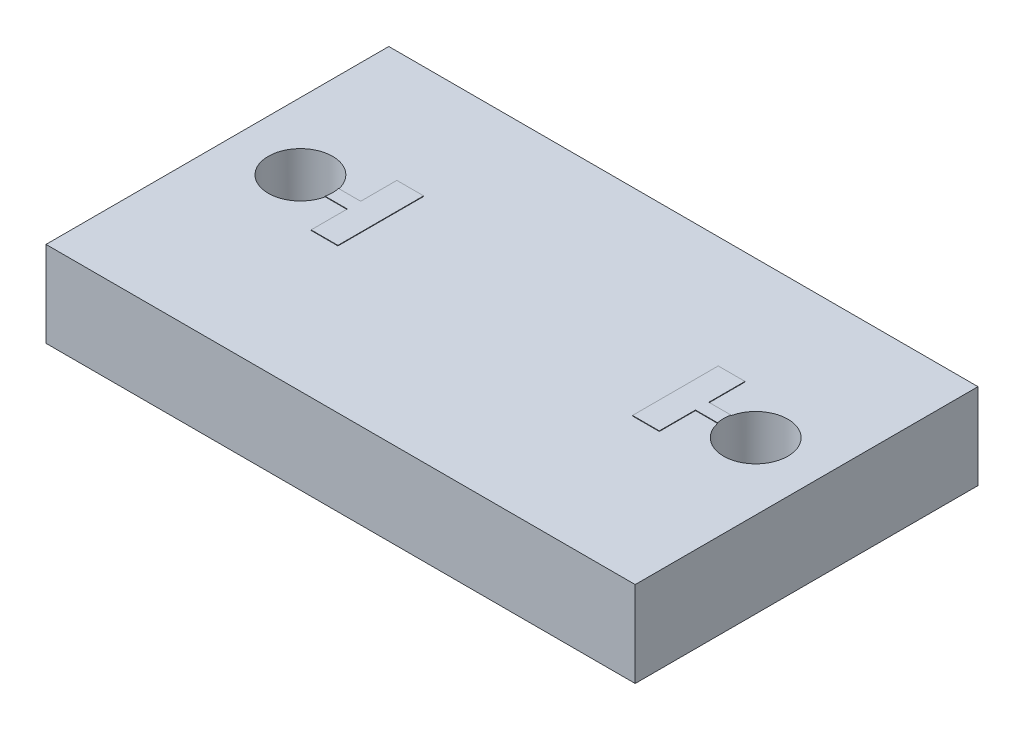
SolidWorks part; units mm, degrees
ref_plane "Front Plane" through (0, 0, 0) normal (0, 0, 1) x (1, 0, 0)
ref_plane "Top Plane" through (0, 0, 0) normal (0, 1, 0) x (1, 0, 0)
ref_plane "Right Plane" through (0, 0, 0) normal (1, 0, 0) x (0, 0, -1)
sketch "Sketch1" plane through (0, 0, 0) normal (0, 1, 0) x (1, 0, 0)
  line L1 (-5.5, -2) -> (5.5, -2)
  line L2 (-5.5, -2) -> (-5.5, 2)
  line L3 (-5.5, 2) -> (5.5, 2)
  line L4 (5.5, -2) -> (5.5, 2)
  line L5 (-5.5, -2) -> (5.5, 2) construction
  line L6 (-5.5, 2) -> (5.5, -2) construction
  point P0 (0, 0)
  dimension "D1" = 4
  dimension "D2" = 11
extrude "Boss-Extrude1" add sketch "Sketch1" along normal blind 1.6
sketch "Sketch2" plane through (0, 1.6, 0) normal (0, 1, 0) x (1, 0, 0)
  line L0 (0, -2) -> (0, 2) construction
  line L1 (-5.5, -2) -> (5.5, -2) construction
  line L2 (5.5, 2) -> (-5.5, 2) construction
  line L3 (-3.25, 0.8) -> (-2.75, 0.8)
  line L8 (0, 0) -> (3, 0)
  line L9 (-2.75, -0.8) -> (-2.75, 0.8)
  line L10 (3.25, -0.8) -> (2.75, -0.8)
  line L11 (3.25, -0.8) -> (3.25, 0.8)
  line L12 (3.25, 0.8) -> (2.75, 0.8)
  line L13 (2.75, -0.8) -> (2.75, 0.8)
  line L14 (3.25, -0.8) -> (2.75, 0.8) construction
  line L15 (3.25, 0.8) -> (2.75, -0.8) construction
  line L16 (-3.25, -0.8) -> (-2.75, -0.8)
  line L17 (-3.25, -0.8) -> (-3.25, 0.8)
  dimension "D3" = 3
  dimension "D4" = 0.5
  dimension "D5" = 1.6
sketch "Sketch3" plane through (0, 1.6, 0) normal (0, 1, 0) x (1, 0, 0)
  line L0 (0, -2) -> (0, 2) construction
  line L1 (4.25, 0) -> (4.25, 1) construction
  line L2 (3.65, 0) -> (3.65, 1)
  line L3 (4.85, 0) -> (4.85, 1)
  line L4 (-4.25, 0) -> (-4.25, 1) construction
  line L5 (-3.65, 0) -> (-3.65, 1)
  line L6 (-4.85, 0) -> (-4.85, 1)
  line L7 (5.5, 2) -> (-5.5, 2) construction
  line L8 (-5.5, -2) -> (5.5, -2) construction
  circle A0 centre (4.25, 0) radius 0.6
  circle A1 centre (-4.25, 0) radius 0.6
  arc A2 (3.65, 0) -> (4.85, 0) centre (4.25, 0) ccw
  arc A3 (4.85, 1) -> (3.65, 1) centre (4.25, 1) ccw
  arc A4 (-3.65, 0) -> (-4.85, 0) centre (-4.25, 0) cw
  arc A5 (-4.85, 1) -> (-3.65, 1) centre (-4.25, 1) cw
  point P10 (4.25, 0.5)
  point P17 (-4.25, 0.5)
  dimension "D1" = 1.2
  dimension "D5" = 1
  dimension "D2" = 1.25
  dimension "D3" = 4.25
  dimension "D4" = 1.2
extrude "Cut-Extrude1" cut sketch "Sketch3" against normal blind 1.6 contours A0 | A1
extrude "Boss-Extrude2" add sketch "Sketch2" along normal blind 0.01
sketch "Sketch4" plane through (0, 1.6, 0) normal (0, 1, 0) x (1, 0, 0)
  line L0 (3.25, -0.8) -> (3.25, 0.8) construction
  line L1 (5.25, -0.125) -> (3.25, -0.125)
  line L2 (5.25, -0.125) -> (5.25, 0.125)
  line L3 (5.25, 0.125) -> (3.25, 0.125)
  line L4 (3.25, -0.125) -> (3.25, 0.125)
  line L5 (5.25, -0.125) -> (3.25, 0.125) construction
  line L6 (5.25, 0.125) -> (3.25, -0.125) construction
  line L7 (0, 0) -> (0, 2) construction
  line L8 (5.5, 2) -> (-5.5, 2) construction
  line L9 (-5.25, 0.125) -> (-3.25, 0.125)
  line L10 (-3.25, -0.125) -> (-3.25, 0.125)
  line L11 (-5.25, -0.125) -> (-3.25, -0.125)
  line L12 (-5.25, -0.125) -> (-5.25, 0.125)
  circle A0 centre (4.25, 0) radius 0.6
  circle A1 centre (-4.25, 0) radius 0.6
  point P0 (4.25, 0)
  line M8 (-3.25, -0.8) -> (-3.25, 0.8)
  line M14 (3.25, 0.8) -> (3.25, -0.8)
  circle M15 centre (4.25, 0) radius 0.6
  circle M16 centre (-4.25, 0) radius 0.6
  dimension "D2" = 1.2
  dimension "D1" = 0.25
extrude "Boss-Extrude3" add sketch "Sketch4" along normal blind 0.01 contours L3 L1 M15 M14 | L11 L9 M16 M8
sketch "Sketch5" plane through (0, 0, 2) normal (0, 0, 1) x (1, 0, 0)
  line L1 (-5.5, 1.6) -> (5.5, 1.6)
  line L2 (-5.5, 1.6) -> (-5.5, 0)
  line L3 (-5.5, 0) -> (5.5, 0)
  line L4 (5.5, 1.6) -> (5.5, 0)
extrude "Boss-Extrude4" add sketch "Sketch5" along normal blind 1.5
sketch "Sketch6" plane through (0, 0, -2) normal (0, 0, -1) x (-1, 0, 0)
  line L1 (5.5, 1.6) -> (-5.5, 1.6)
  line L2 (5.5, 1.6) -> (5.5, 0)
  line L3 (5.5, 0) -> (-5.5, 0)
  line L4 (-5.5, 1.6) -> (-5.5, 0)
extrude "Boss-Extrude5" add sketch "Sketch6" along normal blind 0.9
